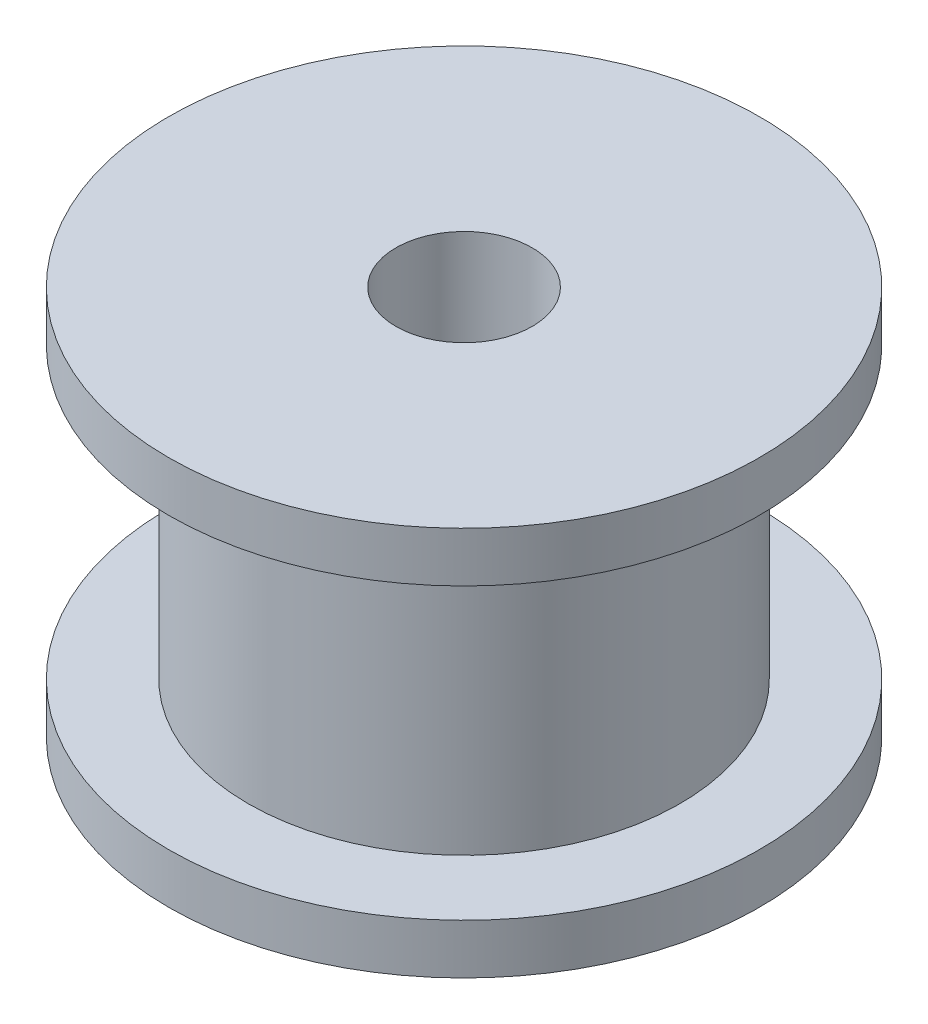
SolidWorks part; units mm, degrees
ref_plane "Front Plane" through (0, 0, 0) normal (0, 0, 1) x (1, 0, 0)
ref_plane "Top Plane" through (0, 0, 0) normal (0, 1, 0) x (1, 0, 0)
ref_plane "Right Plane" through (0, 0, 0) normal (1, 0, 0) x (0, 0, -1)
sketch "Sketch1" plane through (0, 0, 0) normal (0, 1, 0) x (1, 0, 0)
  circle A0 centre (0, 0) radius 6.5
  dimension "D1" = 13
extrude "Boss-Extrude1" add sketch "Sketch1" along normal blind 1.1
sketch "Sketch2" plane through (0, 1.1, 0) normal (0, 1, 0) x (1, 0, 0)
  circle A0 centre (0, 0) radius 4.75
  dimension "D1" = 9.5
extrude "Boss-Extrude2" add sketch "Sketch2" along normal blind 6.37
sketch "Sketch3" plane through (0, 7.47, 0) normal (0, 1, 0) x (1, 0, 0)
  circle A0 centre (0, 0) radius 6.5
  circle A1 centre (0, 0) radius 6.5 construction
extrude "Boss-Extrude3" add sketch "Sketch3" along normal blind 1.1
sketch "Sketch4" plane through (0, 8.57, 0) normal (0, 1, 0) x (1, 0, 0)
  circle A0 centre (0, 0) radius 1.5
  dimension "D1" = 3
extrude "Cut-Extrude1" cut sketch "Sketch4" against normal through all
